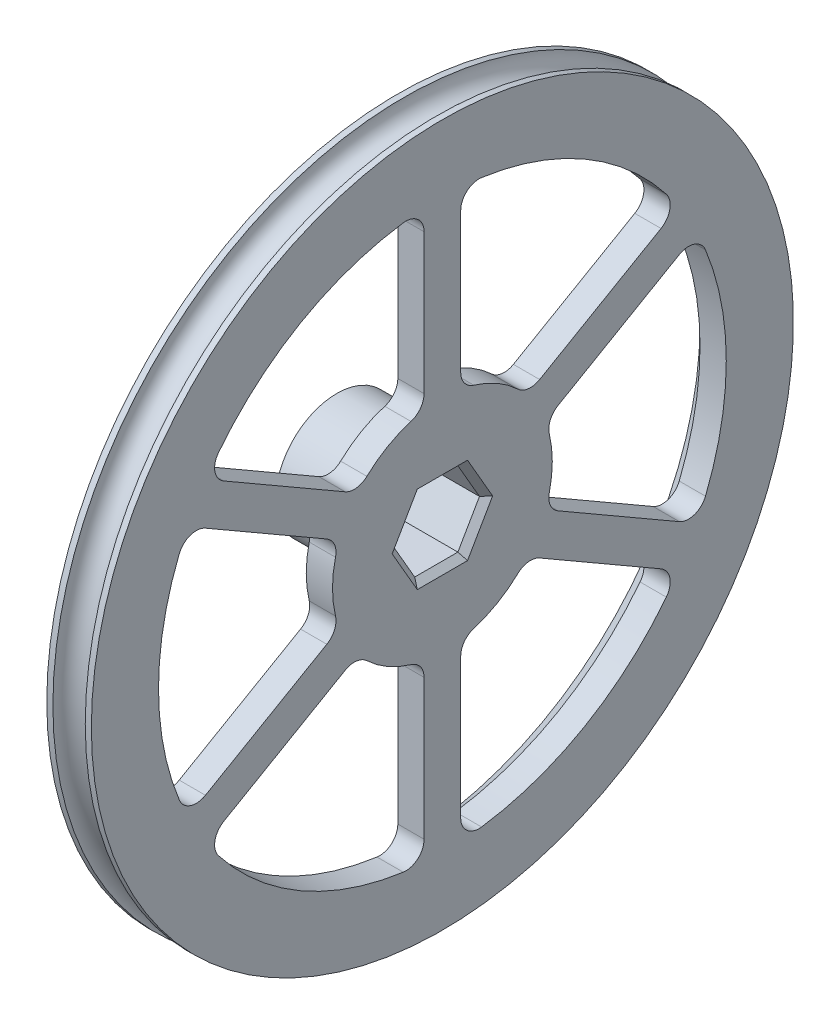
SolidWorks part; units mm, degrees
ref_plane "Front Plane" through (0, 0, 0) normal (0, 0, 1) x (1, 0, 0)
ref_plane "Top Plane" through (0, 0, 0) normal (0, 1, 0) x (1, 0, 0)
ref_plane "Right Plane" through (0, 0, 0) normal (1, 0, 0) x (0, 0, -1)
sketch "Sketch1" plane through (0, 0, 0) normal (0, 1, 0) x (1, 0, 0)
  line L0 (0, 0) -> (0, 57.5) construction
  line L1 (2.65, 0) -> (2.65, 57.5) construction
  line L2 (-2.65, 0) -> (-2.65, 11) construction
  line L3 (3.65, 0) -> (3.65, 57.5)
  line L4 (-3.65, 0) -> (-3.65, 10)
  line L5 (-3.65, 57.5) -> (3.65, 57.5)
  line L6 (-3.65, 0) -> (3.65, 0)
  line L7 (-3.65, 49.5) -> (-0.65, 46.5)
  line L12 (-0.65, 46.5) -> (-0.65, 16.5)
  line L14 (-3.65, 49.5) -> (-3.65, 57.5)
  line L15 (-3.65, 0) -> (-3.65, 57.5) construction
  line L16 (-2.65, 48.5) -> (-2.65, 57.5) construction
  line L17 (-2.65, 0) -> (-2.65, 57.5) construction
  line L18 (-0.65, 16.5) -> (-0.65, 13)
  line L19 (-0.65, 13) -> (-3.65, 10)
  circle A0 centre (0, 57.5) radius 2.65 construction
  dimension "D1" = 2.65
  dimension "D2" = 2.65
  dimension "D3" = 1
  dimension "D4" = 1
revolve "Revolve1" add sketch "Sketch1" angle 360 about L6
sketch "Sketch2" plane through (0, 0, 0) normal (0, 1, 0) x (1, 0, 0)
  line L0 (-3.65, 57.5) -> (3.65, 57.5) construction
  line L1 (-3.65, 57.5) -> (-3.65, -57.5) construction
  line L2 (-3.65, 0) -> (3.65, 0) construction
  line L3 (3.65, -57.5) -> (3.65, 57.5) construction
  circle A0 centre (0, 57.5) radius 2.65
revolve "Cut-Revolve1" cut sketch "Sketch2" angle 360 about L2
sketch "Sketch4" plane through (3.65, 0, 0) normal (1, 0, 0) x (0, 0, -1)
  line L1 (7.0725, 0) -> (3.5363, 6.125)
  line L2 (3.5363, 6.125) -> (-3.5363, 6.125)
  line L3 (-3.5363, 6.125) -> (-7.0725, 0)
  line L4 (-7.0725, 0) -> (-3.5363, -6.125)
  line L5 (-3.5363, -6.125) -> (3.5363, -6.125)
  line L6 (3.5363, -6.125) -> (7.0725, 0)
  circle A0 centre (0, 0) radius 6.125 construction
extrude "Cut-Extrude1" cut sketch "Sketch4" against normal blind 5
sketch "Sketch5" plane through (-3.65, 0, 0) normal (-1, 0, 0) x (0, 0, 1)
  circle A0 centre (0, 0) radius 2
extrude "Cut-Extrude2" cut sketch "Sketch5" against normal blind 5
sketch "Sketch6" plane through (-3.65, 0, 0) normal (-1, 0, 0) x (0, 0, 1)
  circle A0 centre (0, 0) radius 10
  circle A1 centre (0, 0) radius 2 construction
  circle A2 centre (0, 0) radius 2
extrude "Boss-Extrude1" add sketch "Sketch6" along normal blind 10
sketch "Sketch7" plane through (-1.35, 0, 0) normal (1, 0, 0) x (0, 0, -1)
  line L6 (3.5363, -6.125) -> (7.0725, 0)
  line L7 (7.0725, 0) -> (3.5363, 6.125)
  line L8 (3.5363, 6.125) -> (-3.5363, 6.125)
  line L9 (-3.5363, 6.125) -> (-7.0725, 0)
  line L10 (-7.0725, 0) -> (-3.5363, -6.125)
  line L11 (-3.5363, -6.125) -> (3.5363, -6.125)
  line L12 (3.5363, -6.125) -> (7.0725, 0)
  line L13 (7.0725, 0) -> (3.5363, 6.125)
  line L14 (3.5363, 6.125) -> (-3.5363, 6.125)
  line L15 (-3.5363, 6.125) -> (-7.0725, 0)
  line L16 (-7.0725, 0) -> (-3.5363, -6.125)
  line L17 (-3.5363, -6.125) -> (3.5363, -6.125)
  dimension "D1" = 0
extrude "Cut-Extrude3" cut sketch "Sketch7" against normal blind 10
sketch "Sketch8" plane through (-0.65, 0, 0) normal (-1, 0, 0) x (0, 0, 1)
  line L0 (14.0885, 11.5981) -> (38.6863, 25.7996)
  line L1 (3, 18) -> (3, 46.4031)
  line L2 (-3, 18) -> (-3, 46.4031)
  line L3 (-3, 18) -> (-3, 17.7482)
  line L4 (3, 18) -> (3, 17.7482)
  line L5 (17.0885, 6.4019) -> (41.6863, 20.6035)
  line L6 (14.0885, 11.5981) -> (13.8704, 11.4722)
  line L7 (17.0885, 6.4019) -> (16.8704, 6.276)
  line L8 (17.0885, -6.4019) -> (41.6863, -20.6035)
  line L9 (14.0885, -11.5981) -> (38.6863, -25.7996)
  line L10 (17.0885, -6.4019) -> (16.8704, -6.276)
  line L11 (14.0885, -11.5981) -> (13.8704, -11.4722)
  line L12 (3, -18) -> (3, -46.4031)
  line L13 (-3, -18) -> (-3, -46.4031)
  line L14 (3, -18) -> (3, -17.7482)
  line L15 (-3, -18) -> (-3, -17.7482)
  line L16 (-14.0885, -11.5981) -> (-38.6863, -25.7996)
  line L17 (-17.0885, -6.4019) -> (-41.6863, -20.6035)
  line L18 (-14.0885, -11.5981) -> (-13.8704, -11.4722)
  line L19 (-17.0885, -6.4019) -> (-16.8704, -6.276)
  line L20 (-17.0885, 6.4019) -> (-41.6863, 20.6035)
  line L21 (-14.0885, 11.5981) -> (-38.6863, 25.7996)
  line L22 (-17.0885, 6.4019) -> (-16.8704, 6.276)
  line L23 (-14.0885, 11.5981) -> (-13.8704, 11.4722)
  arc A0 (-16.8704, 6.276) -> (-16.8704, -6.276) centre (0, 0) ccw
  circle A1 centre (0, 0) radius 46.5 construction
  arc A2 (-41.6863, 20.6035) -> (-41.6863, -20.6035) centre (0, 0) ccw
  arc A3 (-3, 17.7482) -> (-13.8704, 11.4722) centre (0, 0) ccw
  arc A4 (-3, 46.4031) -> (-38.6863, 25.7996) centre (0, 0) ccw
  arc A5 (13.8704, 11.4722) -> (3, 17.7482) centre (0, 0) ccw
  arc A6 (38.6863, 25.7996) -> (3, 46.4031) centre (0, 0) ccw
  arc A7 (16.8704, -6.276) -> (16.8704, 6.276) centre (0, 0) ccw
  arc A8 (41.6863, -20.6035) -> (41.6863, 20.6035) centre (0, 0) ccw
  arc A9 (3, -17.7482) -> (13.8704, -11.4722) centre (0, 0) ccw
  arc A10 (-13.8704, -11.4722) -> (-3, -17.7482) centre (0, 0) ccw
  arc A11 (-38.6863, -25.7996) -> (-3, -46.4031) centre (0, 0) ccw
  arc A12 (3, -46.4031) -> (38.6863, -25.7996) centre (0, 0) ccw
  dimension "D1" = 6
extrude "Cut-Extrude4" cut sketch "Sketch8" against normal blind 90
fillet "Fillet1" radius 3 24 edges at (1.5, 6.276, -16.8704) (1.5, -6.276, -16.8704) (1.5, -20.6035, -41.6863) (1.5, -25.7996, -38.6863) (1.5, -11.4722, -13.8704) (1.5, -17.7482, -3) (1.5, -46.4031, -3) (1.5, -46.4031, 3) (1.5, -17.7482, 3) (1.5, -11.4722, 13.8704) (1.5, -25.7996, 38.6863) (1.5, -20.6035, 41.6863) (1.5, -6.276, 16.8704) (1.5, 6.276, 16.8704) (1.5, 20.6035, 41.6863) (1.5, 25.7996, 38.6863) (1.5, 11.4722, 13.8704) (1.5, 17.7482, 3) (1.5, 46.4031, 3) (1.5, 46.4031, -3) (1.5, 17.7482, -3) (1.5, 11.4722, -13.8704) (1.5, 20.6035, -41.6863) (1.5, 25.7996, -38.6863)
chamfer "Chamfer1" distance 1 angle 45 6 edges at (3.65, -3.0625, 5.3044) (3.65, -6.125, 0) (3.65, -3.0625, -5.3044) (3.65, 3.0625, -5.3044) (3.65, 6.125, 0) (3.65, 3.0625, 5.3044)
